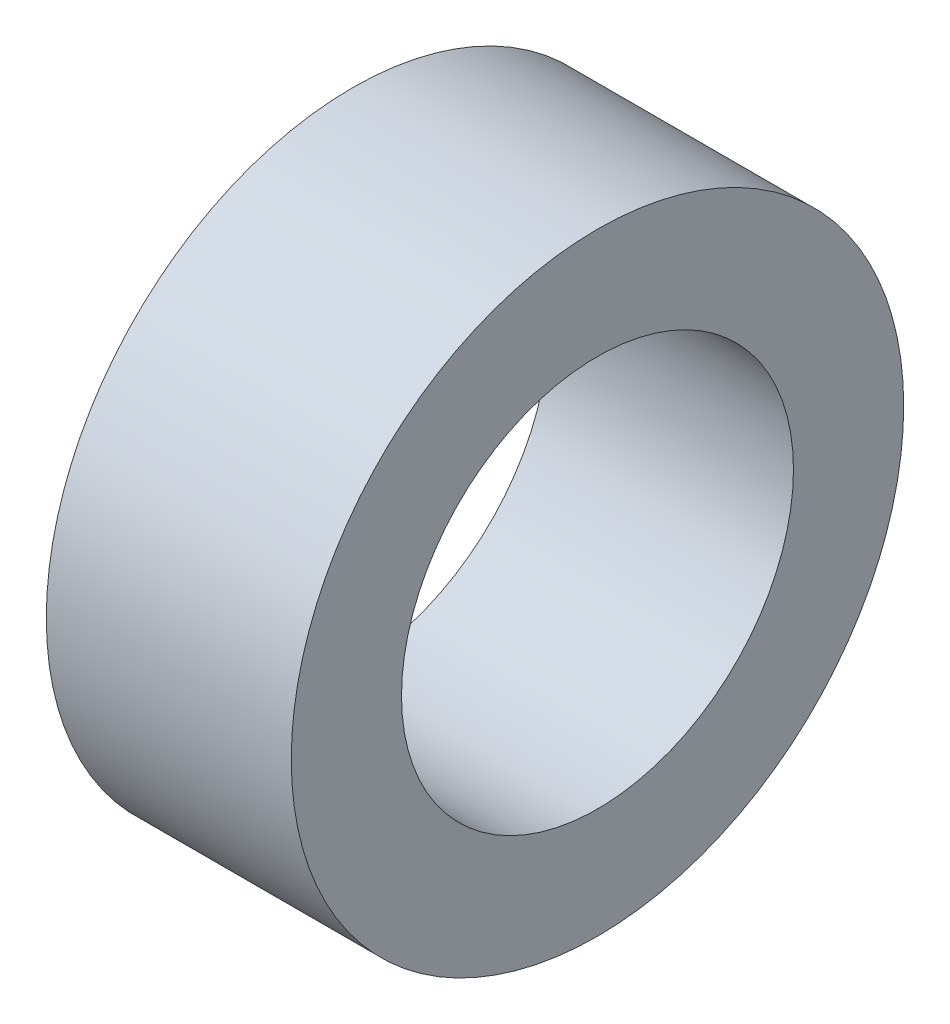
SolidWorks part; units mm, degrees
material "POM Acetal Copolymer"
ref_plane "Front Plane" through (0, 0, 0) normal (0, 0, 1) x (1, 0, 0)
ref_plane "Top Plane" through (0, 0, 0) normal (0, 1, 0) x (1, 0, 0)
ref_plane "Right Plane" through (0, 0, 0) normal (1, 0, 0) x (0, 0, -1)
sketch "Sketch1" plane through (0, 0, 0) normal (1, 0, 0) x (0, 0, -1)
  circle A0 centre (0, 0) radius 1.6
  circle A1 centre (0, 0) radius 2.5
  dimension "D1" = 3.2
  dimension "D2" = 5
extrude "Boss-Extrude1" add sketch "Sketch1" along normal blind 2
